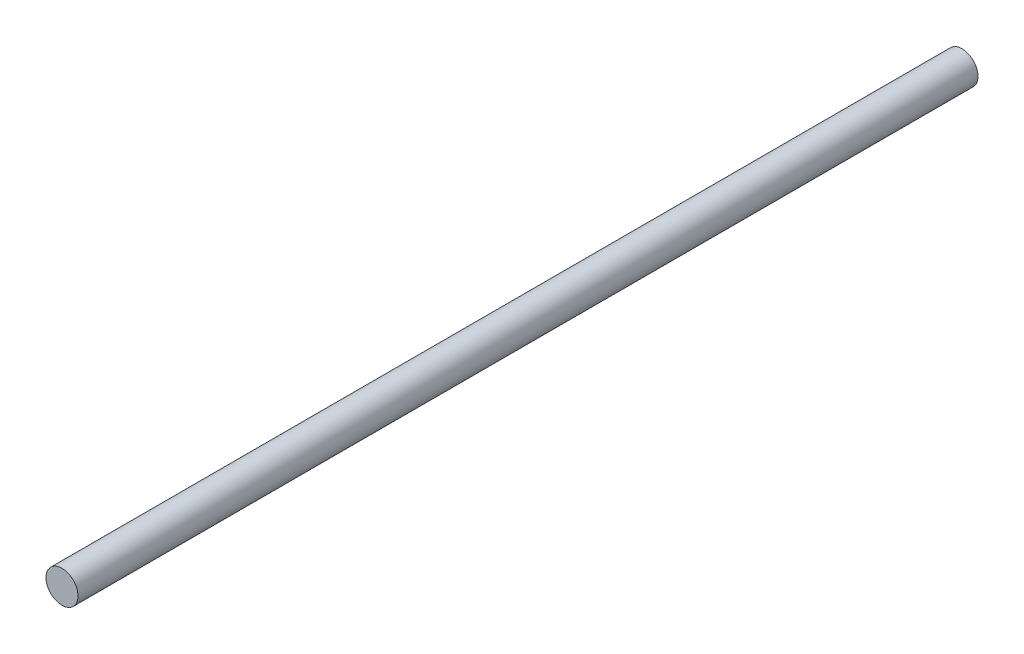
SolidWorks part; units mm, degrees
material "Pure Silver"
ref_plane "前视基准面" through (0, 0, 0) normal (0, 0, 1) x (1, 0, 0)
ref_plane "上视基准面" through (0, 0, 0) normal (0, 1, 0) x (1, 0, 0)
ref_plane "右视基准面" through (0, 0, 0) normal (1, 0, 0) x (0, 0, -1)
other "Configuration Table"
sketch "Sketch1" plane through (0, 0, 0) normal (0, 0, 1) x (1, 0, 0)
  circle A0 centre (0, 0) radius 4.45
  dimension "D1" = 8.9
extrude "Boss-Extrude1" add sketch "Sketch1" along normal blind 250
